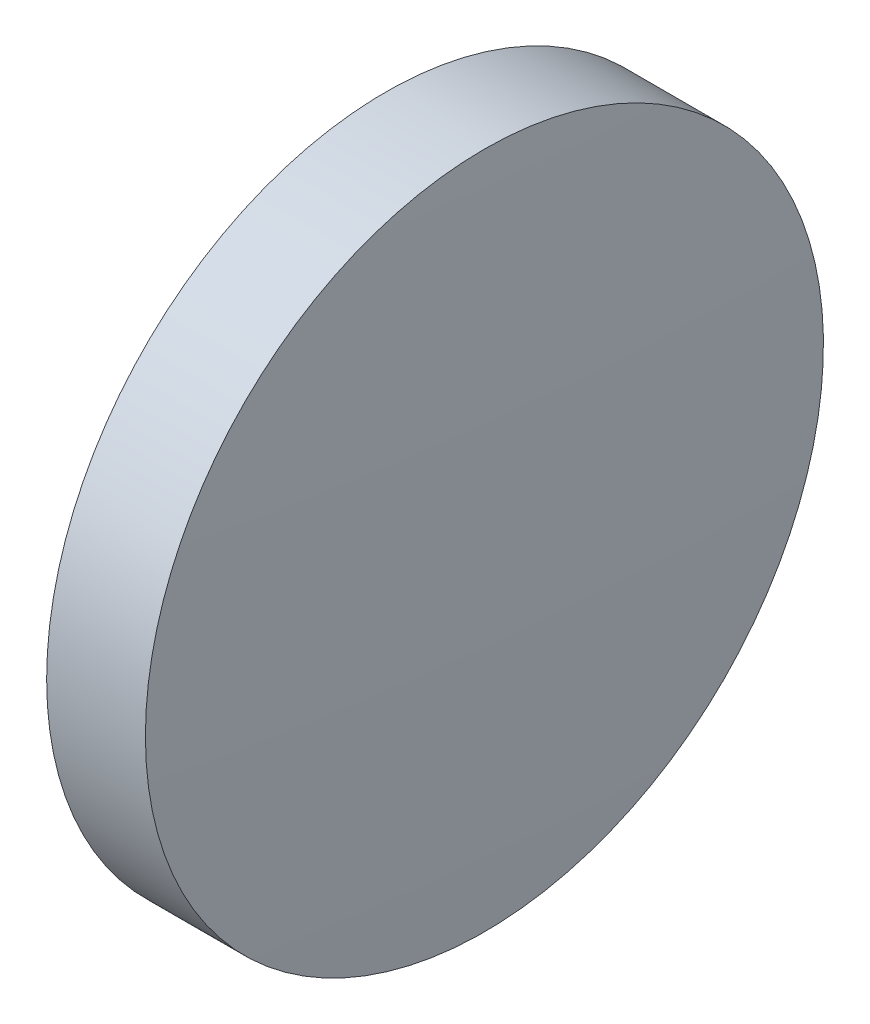
SolidWorks part; units mm, degrees
ref_plane "前视基准面" through (0, 0, 0) normal (0, 0, 1) x (1, 0, 0)
ref_plane "上视基准面" through (0, 0, 0) normal (0, 1, 0) x (1, 0, 0)
ref_plane "右视基准面" through (0, 0, 0) normal (1, 0, 0) x (0, 0, -1)
sketch "草图1" plane through (0, 0, 0) normal (0, 0, 1) x (1, 0, 0)
  line L0 (110.1654, 65.2336) -> (128.9614, 65.2336) construction
  line L1 (115.7646, 65.2336) -> (115.7646, 77.9336)
  line L2 (119.7646, 65.2336) -> (115.7646, 65.2336)
  line L5 (115.7646, 77.9336) -> (119.4646, 77.9336)
  arc A0 (119.7646, 65.2336) -> (119.4646, 77.9336) centre (-149.2021, 65.2336) ccw
revolve "旋转1" add sketch "草图1" angle 360 about L0
